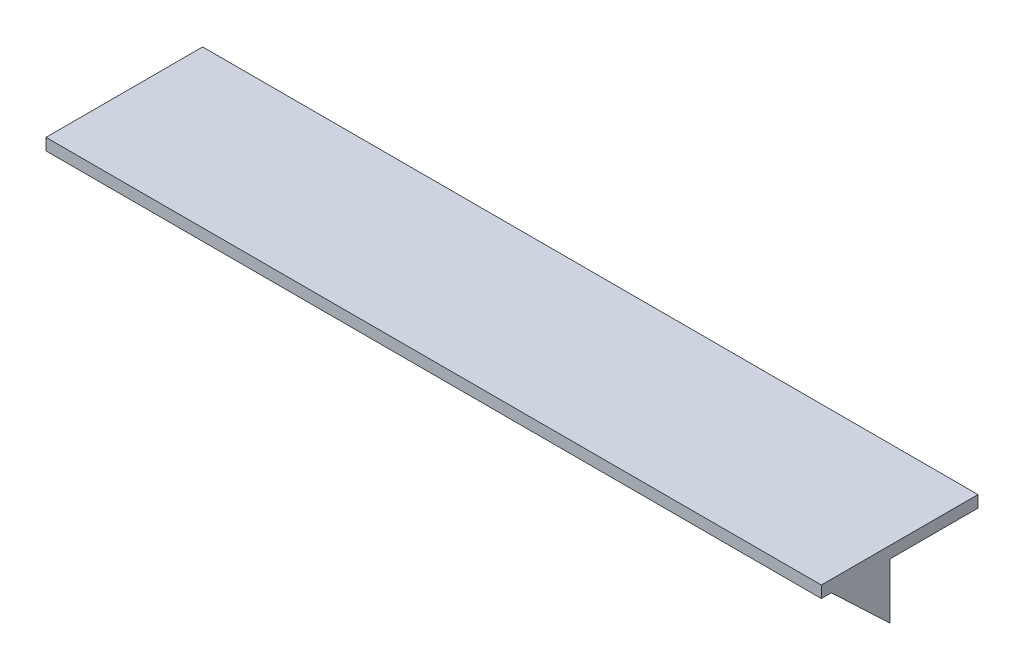
SolidWorks part; units mm, degrees
ref_plane "Front Plane" through (0, 0, 0) normal (0, 0, 1) x (1, 0, 0)
ref_plane "Top Plane" through (0, 0, 0) normal (0, 1, 0) x (1, 0, 0)
ref_plane "Right Plane" through (0, 0, 0) normal (1, 0, 0) x (0, 0, -1)
sketch "Sketch1" plane through (0, 0, 0) normal (0, 1, 0) x (1, 0, 0)
  line L1 (-99, -20) -> (99, -20)
  line L2 (-99, -20) -> (-99, 20)
  line L3 (-99, 20) -> (99, 20)
  line L4 (99, -20) -> (99, 20)
  line L5 (-99, -20) -> (99, 20) construction
  line L6 (-99, 20) -> (99, -20) construction
  point P0 (0, 0)
  point P5 (0, 0)
  dimension "D1" = 198
  dimension "D2" = 40
extrude "Boss-Extrude1" add sketch "Sketch1" along normal blind 3
ref_plane "Plane1" through (-99, 0, 0) normal (-1, 0, 0) x (0, 0, 1)
sketch "Sketch2" plane through (-99, 0, 2.5229) normal (-1, 0, 0) x (0, 0, 1)
  line L0 (0, 0) -> (0, -14.1615)
  line L1 (0, -14.1615) -> (14.9251, 0)
  line L3 (14.9251, 0) -> (0, 0)
extrude "Boss-Extrude2" add sketch "Sketch2" against normal blind 198
